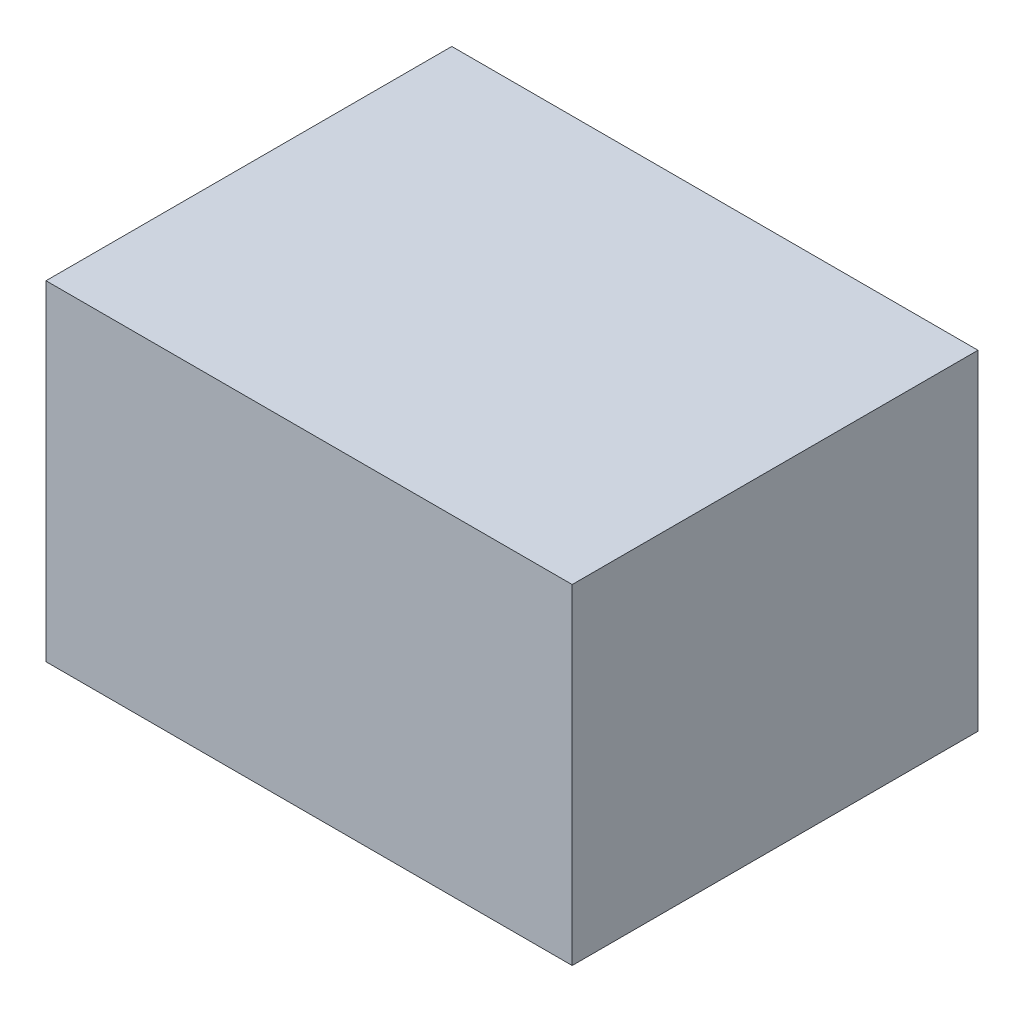
SolidWorks part; units mm, degrees
ref_plane "Front Plane" through (0, 0, 0) normal (0, 0, 1) x (1, 0, 0)
ref_plane "Top Plane" through (0, 0, 0) normal (0, 1, 0) x (1, 0, 0)
ref_plane "Right Plane" through (0, 0, 0) normal (1, 0, 0) x (0, 0, -1)
sketch "ButtonBase Sketch" plane through (0, 0, 0) normal (0, 1, 0) x (1, 0, 0)
  line L1 (0, 0) -> (5.9, 0)
  line L2 (0, 0) -> (0, 4.55)
  line L3 (0, 4.55) -> (5.9, 4.55)
  line L4 (5.9, 0) -> (5.9, 4.55)
  dimension "ButtonBase Width" = 5.9
  dimension "ButtonBase Length" = 4.55
extrude "ButtonBase Extrude" add sketch "ButtonBase Sketch" along normal blind 3.7
